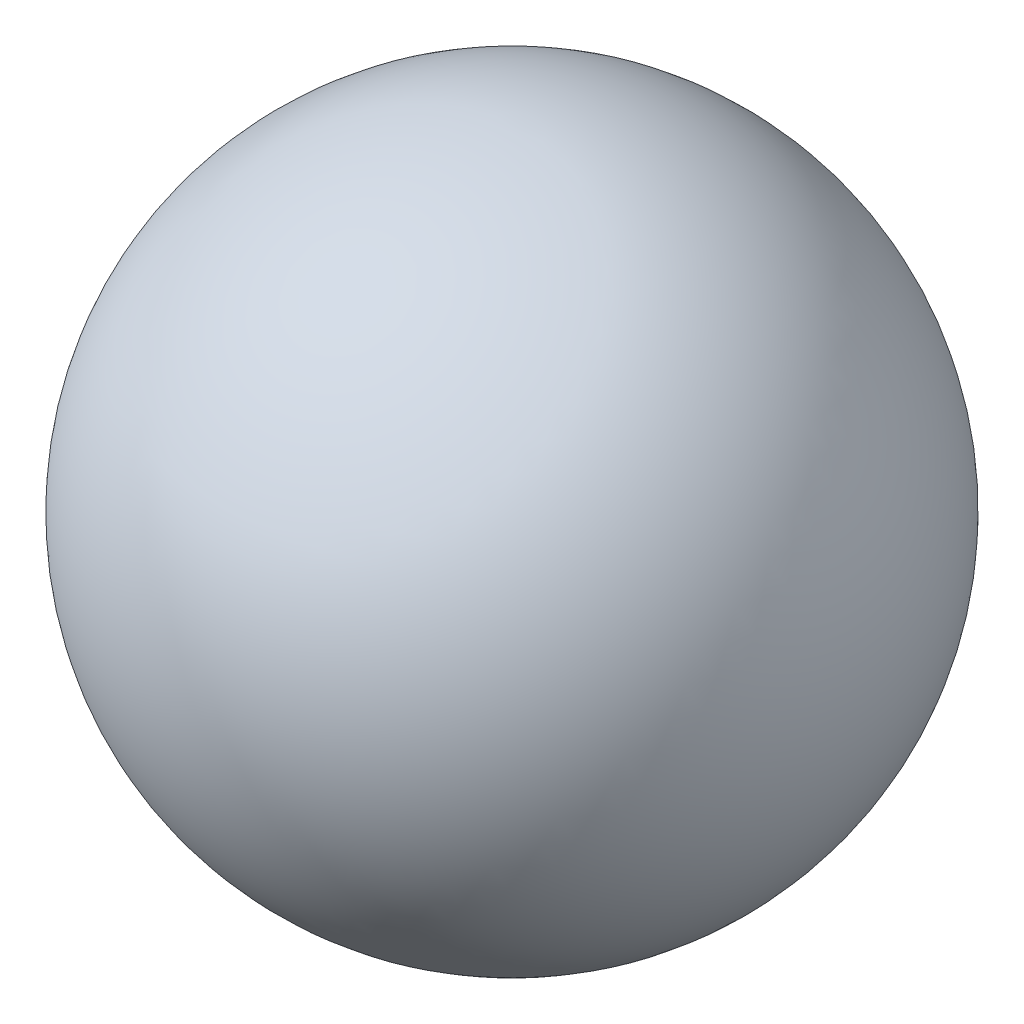
SolidWorks part; units mm, degrees
material "Al2O3"
ref_plane "Front Plane" through (0, 0, 0) normal (0, 0, 1) x (1, 0, 0)
ref_plane "Top Plane" through (0, 0, 0) normal (0, 1, 0) x (1, 0, 0)
ref_plane "Right Plane" through (0, 0, 0) normal (1, 0, 0) x (0, 0, -1)
sketch "Sketch1" plane through (0, 0, 0) normal (0, 0, 1) x (1, 0, 0)
  line L0 (0, 48.6406) -> (0, 10.7835) construction
  line L1 (0, 1.5875) -> (0, -1.5875)
  arc A0 (0, 1.5875) -> (0, -1.5875) centre (0, 0) cw
  dimension "D1" = 3.175
revolve "Revolve1" add sketch "Sketch1" angle 360 about L0
hole_wizard "1/16 (0.0625) Diameter Hole1" positions "3DSketch1" profile "Sketch3" hole size "1/16" standard "Ansi Inch"
sketch3d "3DSketch1"
  line L0 (0, 0, 0) -> (0, -1.5875, 0)
  point P0 (0, -1.5875, 0)
sketch "Sketch3" plane through (0, -1.5875, 0) normal (1, 0, 0) x (0, 0, -1)
  line L0 (0, 0) -> (0, 2.0617)
  line L1 (0, 2.0617) -> (0.785, 1.59)
  line L2 (0.785, 1.59) -> (0.785, 0)
  line L5 (0.785, 0) -> (0, 0)
  line L10 (0, 2.0617) -> (-0.785, 1.59) construction
  line L11 (0, -6.35) -> (0, 107.95) construction
  dimension "Hole Dia." = 1.57
  dimension "Hole Depth" = 1.59
  dimension "Drill Angle" = 118
ref_plane "Plane1 (mate ref)" through (0, -1.3798, 0) normal (0, 1, 0) x (-1, 0, 0)
